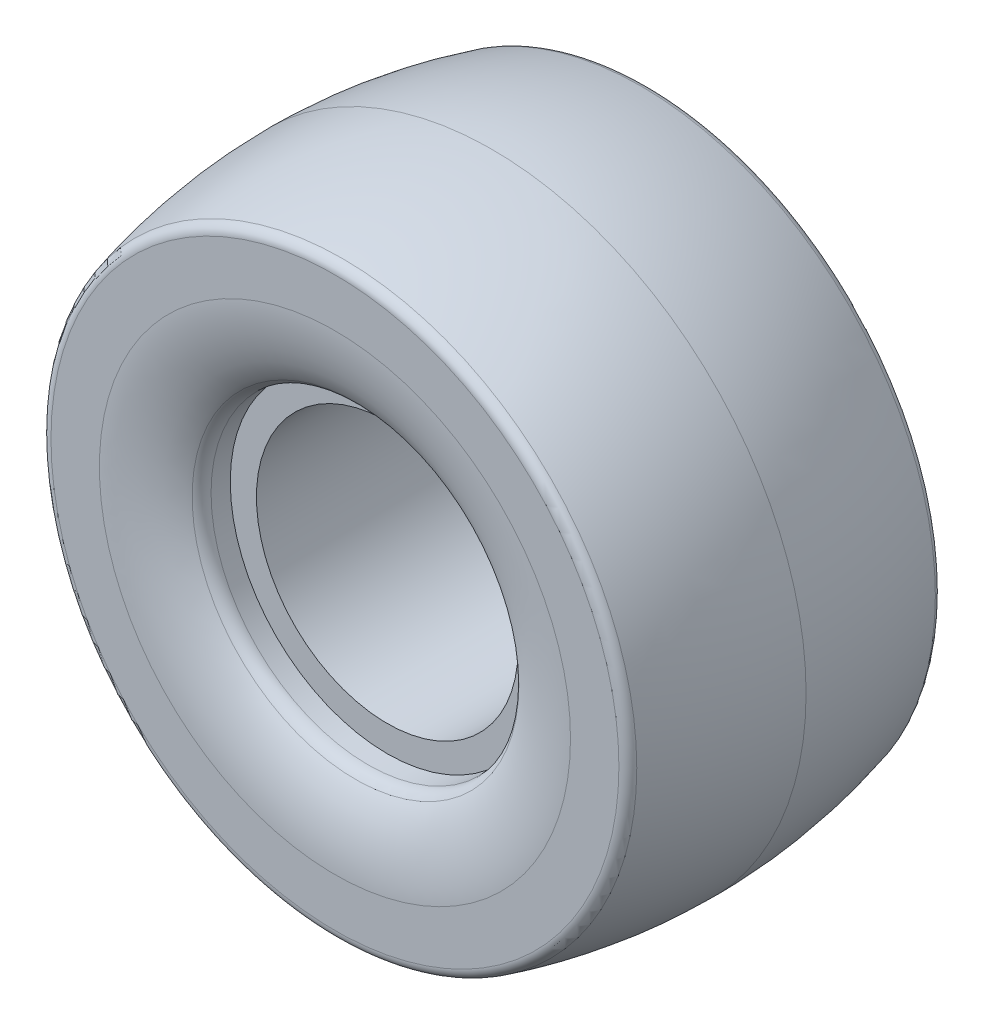
SolidWorks part; units mm, degrees
ref_plane "Front Plane" through (0, 0, 0) normal (0, 0, 1) x (1, 0, 0)
ref_plane "Top Plane" through (0, 0, 0) normal (0, 1, 0) x (1, 0, 0)
ref_plane "Right Plane" through (0, 0, 0) normal (1, 0, 0) x (0, 0, -1)
sketch "Sketch1" plane through (0, 0, 0) normal (1, 0, 0) x (0, 0, -1)
  line L0 (-30, 0) -> (30, 0) construction
  line L1 (0, 0) -> (0, 25) construction
  line L2 (0, 12.5) -> (-20, 12.5) construction
  line L3 (20, 25) -> (-20, 25)
  line L4 (-20, 25) -> (-20, 30)
  line L5 (-20, 30) -> (-23.6685, 30)
  line L6 (-30, 0) -> (-30, 30) construction
  line L7 (-30, 30) -> (-25, 30) construction
  line L8 (-30, 30) -> (-30, 60) construction
  line L9 (-30, 60) -> (0, 60) construction
  line L10 (-30, 38.6754) -> (-30, 51.3246) construction
  line L11 (20, 25) -> (20, 30)
  line L12 (20, 30) -> (23.6685, 30)
  line L13 (30, 54.2456) -> (30, 45)
  line L15 (-30, 60) -> (-33.1825, 60) construction
  line L16 (-33.1825, 60) -> (-33.1825, 55.7698) construction
  line L17 (-33.1825, 55.7698) -> (-30, 55.7698) construction
  line L18 (-33.1825, 55.7698) -> (-33.1825, 45) construction
  line L19 (-33.1825, 45) -> (-30, 45) construction
  line L20 (-30, 54.2456) -> (-30, 45)
  line L21 (0, 60) -> (0, 25) construction
  arc A0 (-30, 54.2456) -> (-28.5179, 56.1774) centre (-28, 54.2456) cw
  arc A1 (-23.6685, 30) -> (-26.0741, 31.2075) centre (-23.6685, 33) cw
  arc A2 (23.6685, 30) -> (26.0741, 31.2075) centre (23.6685, 33) ccw
  arc A3 (30, 54.2456) -> (28.5179, 56.1774) centre (28, 54.2456) ccw
  spline S0 degree 3 poles (-28.5179, 56.1774) (-23.7649, 57.4516) (-14.2589, 59.3629) (-4.753, 60) (0, 60) knots 0.024702 0.024702 0.024702 0.024702 0.262351 0.5 0.5 0.5 0.5
  spline S1 degree 3 poles (-30, 45) (-30, 42.6862) (-29.2604, 37.4316) (-27.2974, 32.8492) (-26.0741, 31.2075) knots 0 0 0 0 0.439021 0.878042 0.878042 0.878042 0.878042
  spline S2 degree 3 poles (30, 45) (30, 42.6862) (29.2604, 37.4316) (27.2974, 32.8492) (26.0741, 31.2075) knots 0 0 0 0 0.439021 0.878042 0.878042 0.878042 0.878042
  spline S3 degree 3 poles (28.5179, 56.1774) (23.7649, 57.4516) (14.2589, 59.3629) (4.753, 60) (0, 60) knots 0.024702 0.024702 0.024702 0.024702 0.262351 0.5 0.5 0.5 0.5
  dimension "D1" = 2
  dimension "D2" = 3
revolve "Revolve1" add sketch "Sketch1" angle 360 about L0
